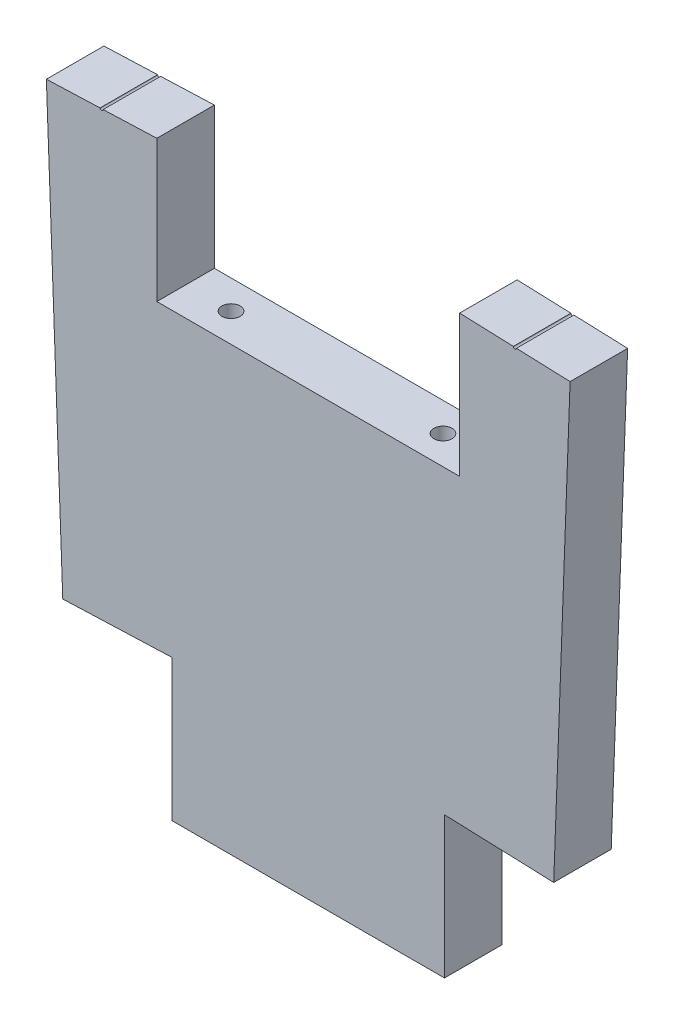
SolidWorks part; units mm, degrees
ref_plane "Front Plane" through (0, 0, 0) normal (0, 0, 1) x (1, 0, 0)
ref_plane "Top Plane" through (0, 0, 0) normal (0, 1, 0) x (1, 0, 0)
ref_plane "Right Plane" through (0, 0, 0) normal (1, 0, 0) x (0, 0, -1)
sketch "Sketch1" plane through (0, 0, 0) normal (0, 0, 1) x (1, 0, 0)
  line L1 (86.489, 32.6481) -> (2523.2123, -57.7618)
  line L2 (2523.2123, -57.7618) -> (2519.4304, -159.6916)
  line L3 (2519.4304, -159.6916) -> (82.707, -69.2817)
  line L4 (82.707, -69.2817) -> (86.489, 32.6481)
  line L5 (2519.4304, -159.6916) -> (120.707, -159.6916) construction
  line L6 (82.707, -70.6916) -> (120.707, -70.6916)
  line L7 (82.707, -70.6916) -> (82.707, -159.6916)
  line L8 (82.707, -159.6916) -> (120.707, -159.6916)
  line L9 (120.707, -70.6916) -> (120.707, -159.6916)
  line L11 (-50, 0) -> (50, 0)
  line L12 (-50, 0) -> (-50, -12.7)
  line L13 (-50, -12.7) -> (50, -12.7)
  line L14 (50, 0) -> (50, -12.7)
  line L22 (0, 0) -> (0, -236.7459) construction
  line L23 (-2519.4304, -159.6916) -> (-120.707, -159.6916) construction
  line L26 (-120.707, -70.6916) -> (-120.707, -159.6916)
  line L27 (-82.707, -159.6916) -> (-120.707, -159.6916)
  line L28 (-82.707, -70.6916) -> (-82.707, -159.6916)
  line L29 (-82.707, -70.6916) -> (-120.707, -70.6916)
  line L30 (-82.707, -69.2817) -> (-86.489, 32.6481)
  line L31 (-2519.4304, -159.6916) -> (-82.707, -69.2817)
  line L32 (-2523.2123, -57.7618) -> (-2519.4304, -159.6916)
  line L33 (-86.489, 32.6481) -> (-2523.2123, -57.7618)
  point P15 (0, 0)
  dimension "D2" = 2438.4
  dimension "D3" = 102
  dimension "D4" = 38
  dimension "D5" = 89
  dimension "D6" = 12.7
  dimension "D7" = 100
sketch "Sketch2" plane through (0, 0, 0) normal (0, 0, 1) x (1, 0, 0)
  line L0 (-50, -12.7) -> (50, -12.7)
  line L1 (-50, -12.7) -> (50, -12.7) construction
  line L2 (50, -12.7) -> (50, 34.002)
  line L4 (50, 34.002) -> (86.489, 32.6481)
  line L5 (86.489, 32.6481) -> (79.3897, -158.6916)
  line L6 (79.3897, -158.6916) -> (-79.3897, -158.6916)
  line L7 (0, -158.6916) -> (0, -12.7) construction
  line L8 (82.707, -159.6916) -> (120.707, -159.6916) construction
  line L9 (-86.489, 32.6481) -> (-79.3897, -158.6916)
  line L10 (-50, 34.002) -> (-86.489, 32.6481)
  line L11 (-50, -12.7) -> (-50, 34.002)
  dimension "D1" = 1
extrude "Boss-Extrude1" add sketch "Sketch2" against normal blind 19
sketch "Sketch4" plane through (0, 0, -19) normal (0, 0, -1) x (-1, 0, 0)
  line L0 (177, -116.8873) -> (45, -111.9897)
  line L1 (45, -111.9897) -> (45, -158.6916)
  line L2 (45, -158.6916) -> (-45, -158.6916)
  line L3 (-45, -158.6916) -> (-45, -111.9897)
  line L4 (-45, -111.9897) -> (-160.8148, -116.2867)
  line L5 (-160.8148, -116.2867) -> (-160.8148, -226.3289)
  line L6 (-160.8148, -226.3289) -> (177, -226.3289)
  line L7 (177, -226.3289) -> (177, -116.8873)
  line L8 (50, -12.7) -> (50, 34.002) construction
  line L9 (-50, 34.002) -> (-50, -12.7) construction
  line L11 (50, 34.002) -> (86.489, 32.6481) construction
  line L12 (79.3897, -158.6916) -> (-79.3897, -158.6916) construction
  line L13 (0, 0) -> (0, -198.7369) construction
  line L14 (-50, 34.002) -> (-50, -12.7) construction
  line L15 (50, -12.7) -> (50, 34.002) construction
  dimension "D1" = 5
  dimension "D2" = 5
extrude "Cut-Extrude1" cut sketch "Sketch4" against normal blind 19
sketch "Sketch5" plane through (0, 0, 0) normal (0, 0, 1) x (1, 0, 0)
  line L0 (81.1882, 51.6055) -> (79.8951, 16.7543) construction
  line L1 (56.6423, 51.2016) -> (55.5023, 20.4756) construction
  dimension "D1" = 6
  dimension "D2" = 6
  dimension "D3" = 24.5141
sketch "Sketch6" plane through (0, -12.7, 0) normal (0, 1, 0) x (1, 0, 0)
  circle A0 centre (35, 9.5) radius 3
  circle A1 centre (-35, 9.5) radius 3
  dimension "D1" = 6
  dimension "D2" = 6
extrude "Cut-Extrude2" cut sketch "Sketch6" against normal blind 10
sketch "Sketch9" plane through (0, 0, -19) normal (0, 0, -1) x (-1, 0, 0)
  line L0 (50, 34.002) -> (86.489, 32.6481) construction
  line L1 (0, 0) -> (0, 66.3846) construction
  circle A0 centre (68.2445, 33.3251) radius 0.5
  circle A1 centre (-68.2445, 33.3251) radius 0.5
  point P4 (68.2445, 33.3251)
  dimension "D1" = 1
extrude "Cut-Extrude3" cut sketch "Sketch9" against normal blind 20
